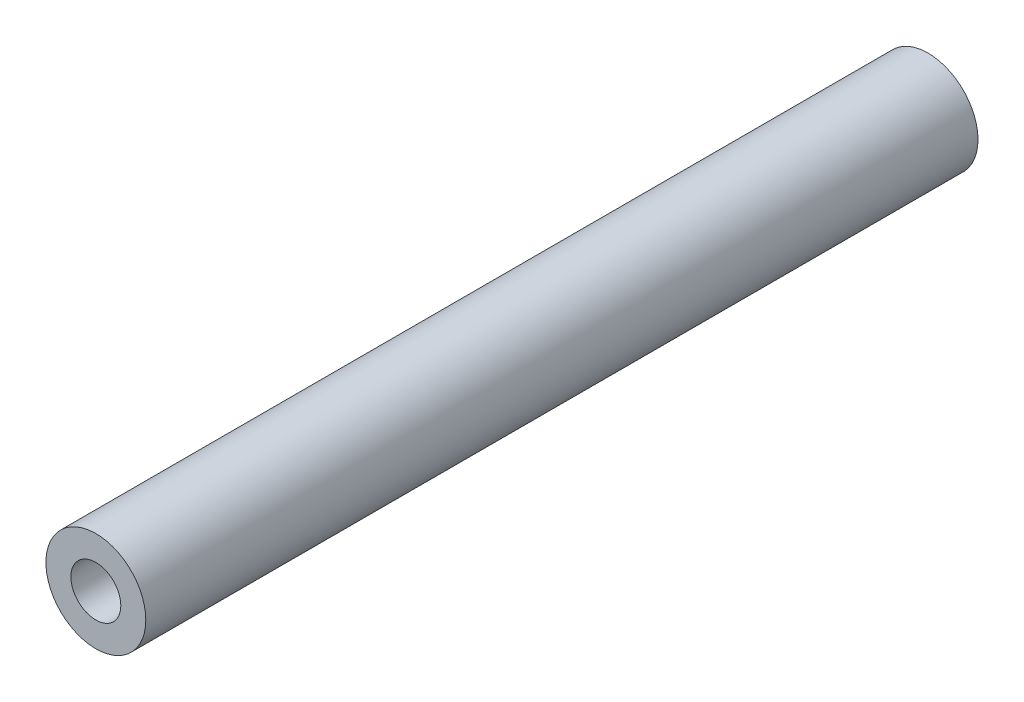
SolidWorks part; units mm, degrees
ref_plane "前视基准面" through (0, 0, 0) normal (0, 0, 1) x (1, 0, 0)
ref_plane "上视基准面" through (0, 0, 0) normal (0, 1, 0) x (1, 0, 0)
ref_plane "右视基准面" through (0, 0, 0) normal (1, 0, 0) x (0, 0, -1)
other "Configuration Table"
sketch "草图2" plane through (0, 0, 0) normal (0, 0, 1) x (1, 0, 0)
  circle A0 centre (-223.0556, 347.7485) radius 30
  circle A1 centre (-223.0556, 347.7485) radius 15
  dimension "D1" = 30
  dimension "D2" = 60
extrude "凸台-拉伸1" add sketch "草图2" along normal blind 500
